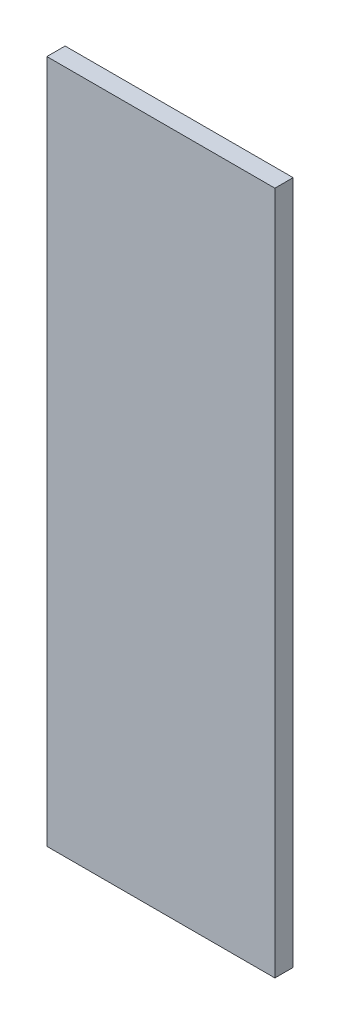
SolidWorks part; units mm, degrees
material "Cardboard"
ref_plane "Front Plane" through (0, 0, 0) normal (0, 0, 1) x (1, 0, 0)
ref_plane "Top Plane" through (0, 0, 0) normal (0, 1, 0) x (1, 0, 0)
ref_plane "Right Plane" through (0, 0, 0) normal (1, 0, 0) x (0, 0, -1)
sketch "Sketch1" plane through (0, 0, 0) normal (0, 0, 1) x (1, 0, 0)
  line L1 (0, 0) -> (50, 0)
  line L2 (0, 0) -> (0, 150)
  line L3 (0, 150) -> (50, 150)
  line L4 (50, 0) -> (50, 150)
  dimension "D1" = 150
  dimension "D2" = 50
extrude "Boss-Extrude1" add sketch "Sketch1" along normal blind 4
